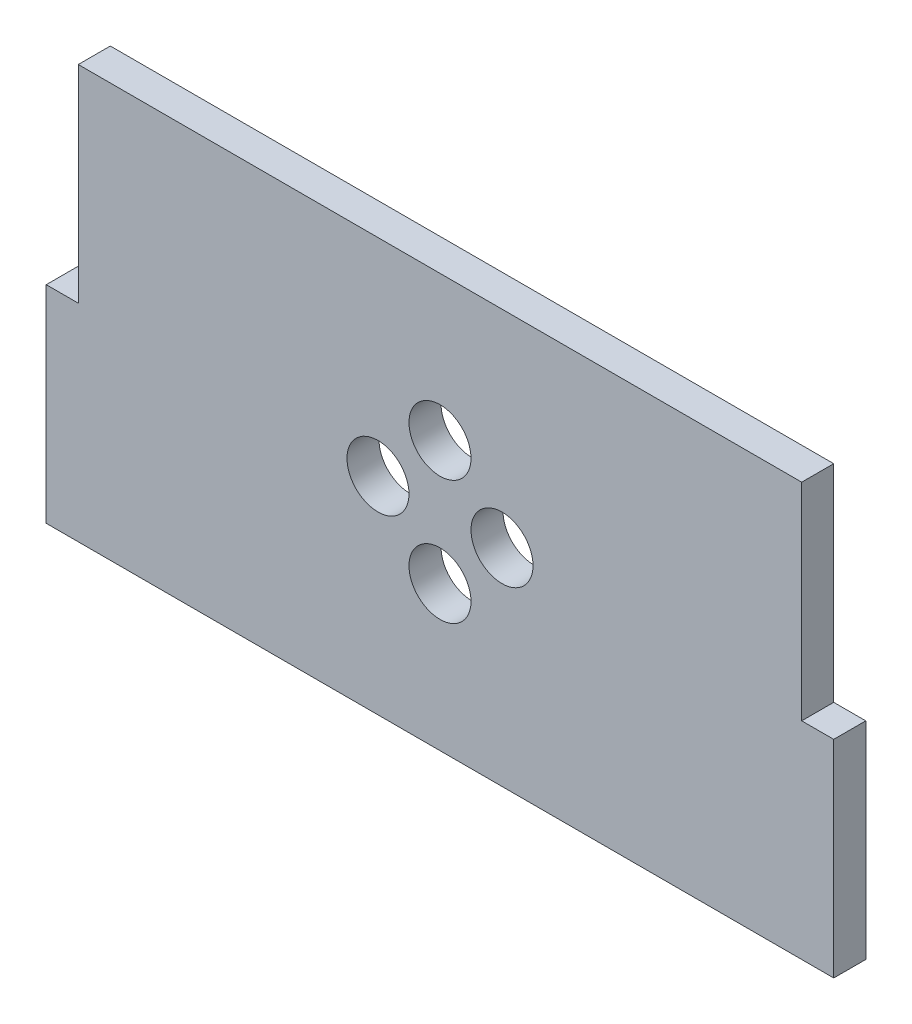
SolidWorks part; units mm, degrees
material "Teak"
ref_plane "Front Plane" through (0, 0, 0) normal (0, 0, 1) x (1, 0, 0)
ref_plane "Top Plane" through (0, 0, 0) normal (0, 1, 0) x (1, 0, 0)
ref_plane "Right Plane" through (0, 0, 0) normal (1, 0, 0) x (0, 0, -1)
sketch "Sketch1" plane through (0, 0, 0) normal (0, 0, 1) x (1, 0, 0)
  line L0 (0, 0) -> (0, 20) construction
  line L1 (-35, -20) -> (35, -20)
  line L2 (-35, -20) -> (-35, 20)
  line L3 (-35, 20) -> (35, 20)
  line L4 (35, -20) -> (35, 20)
  line L5 (-35, -20) -> (35, 20) construction
  line L6 (-35, 20) -> (35, -20) construction
  line L7 (0, 20) -> (0, 0) construction
  line L8 (0, 0) -> (-35, 0) construction
  circle A0 centre (-6, 0) radius 3
  circle A1 centre (0, 6) radius 3
  circle A2 centre (6, 0) radius 3
  circle A3 centre (0, -6) radius 3
  point P0 (0, 0)
  point P20 (0, 0)
  dimension "D3" = 6
  dimension "D4" = 4
  dimension "D1" = 70
  dimension "D2" = 40
  dimension "D5" = 12
  dimension "D6" = 0
extrude "Boss-Extrude1" add sketch "Sketch1" along normal blind 3.1
sketch "Sketch2" plane through (0, 0, 3.1) normal (0, 0, 1) x (1, 0, 0)
  line L0 (35, 0) -> (35, -20)
  line L1 (35, 0) -> (38.1, 0)
  line L2 (35, -20) -> (38.1, -20)
  line L3 (38.1, 0) -> (38.1, -20)
  line L4 (35, -20) -> (35, 20) construction
  line L5 (0, 20) -> (0, 0) construction
  line L6 (35, 20) -> (-35, 20) construction
  line L7 (-38.1, 0) -> (-38.1, -20)
  line L8 (-35, -20) -> (-38.1, -20)
  line L9 (-35, 0) -> (-38.1, 0)
  line L10 (-35, 0) -> (-35, -20)
  dimension "D1" = 3.1
extrude "Boss-Extrude2" add sketch "Sketch2" against normal through all
sketch "Sketch3" plane through (0, 0, 0) normal (0, 0, 1) x (1, 0, 0)
  line L0 (0, 0) -> (0, 20) construction
  line L1 (-23, -20) -> (23, -20)
  line L2 (-23, -20) -> (-23, 20)
  line L3 (-23, 20) -> (23, 20)
  line L4 (23, -20) -> (23, 20)
  line L5 (-23, -20) -> (23, 20) construction
  line L6 (-23, 20) -> (23, -20) construction
  line L7 (0, 20) -> (0, 0) construction
  line L8 (0, 0) -> (-23, 0) construction
  circle A0 centre (-6, 0) radius 3
  circle A1 centre (6, 0) radius 3
  point P0 (0, 0)
  point P20 (0, 0)
  dimension "D3" = 6
  dimension "D4" = 2
  dimension "D1" = 46
  dimension "D2" = 40
  dimension "D6" = 0
sketch "Sketch4" plane through (0, 0, 0) normal (0, 0, 1) x (1, 0, 0)
  line L0 (23, 0) -> (23, -20)
  line L1 (23, 0) -> (26.1, 0)
  line L2 (23, -20) -> (26.1, -20)
  line L3 (26.1, 0) -> (26.1, -20)
  line L5 (0, 20) -> (0, 0) construction
  line L7 (-26.1, 0) -> (-26.1, -20)
  line L8 (-23, -20) -> (-26.1, -20)
  line L9 (-23, 0) -> (-26.1, 0)
  line L10 (-23, 0) -> (-23, -20)
  dimension "D1" = 3.1
extrude "Boss-Extrude3" [suppressed] add sketch "Sketch3" along normal blind 3.1
extrude "Boss-Extrude4" [suppressed] add sketch "Sketch4" along normal through all
equation "\"thick\" = 3.1mm"
equation "\"small_bearing_outer\"=12.9mm"
equation "\"servo1_L\"=40.7mm"
equation "\"servo1_W\"=20.5mm"
equation "\"servo1_H\"=43.5mm"
equation "\"servo1_hL\"=49mm"
equation "\"servo1_hW\"=10mm"
equation "\"servo1_H2\"=27mm"
equation "\"large_bearing_inner\"=2.75in"
equation "\"large_bearing_outer\"=4.75in"
equation "\"large_bearing_thick\"=3/8in"
equation "\"large_bearing_h1\"=3.25in"
equation "\"large_bearing_h2\"=4.25in"
equation "\"D1@Boss-Extrude1\"=\"thick\""
equation "\"D1@Sketch2\"=\"thick\""
equation "\"D1@Boss-Extrude3\"=\"thick\""
